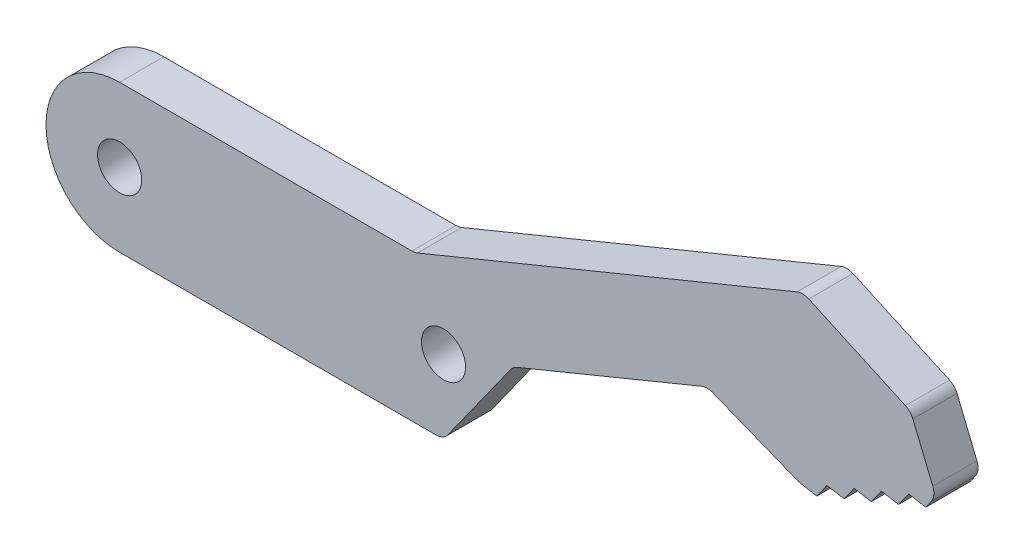
SolidWorks part; units mm, degrees
ref_plane "Front Plane" through (0, 0, 0) normal (0, 0, 1) x (1, 0, 0)
ref_plane "Top Plane" through (0, 0, 0) normal (0, 1, 0) x (1, 0, 0)
ref_plane "Right Plane" through (0, 0, 0) normal (1, 0, 0) x (0, 0, -1)
sketch "Sketch1" plane through (0, 0, 0) normal (0, 0, 1) x (1, 0, 0)
  line L0 (0, 0) -> (22, 0) construction
  line L1 (0, 5) -> (22, 5)
  line L2 (0, -5) -> (22, -5)
  line L3 (20.05, 5) -> (23.9914, -4.5863) construction
  line L4 (20.05, 5) -> (51.4959, 17.929) construction
  line L5 (23.9914, -4.5863) -> (55.4373, 8.3426) construction
  line L6 (51.4959, 17.929) -> (55.4373, 8.3426) construction
  line L7 (20.05, 5) -> (46.409, 15.8375)
  line L8 (46.409, 15.8375) -> (53.7261, 12.5046)
  line L9 (53.7261, 12.5046) -> (55.4373, 8.3426)
  line L10 (55.4373, 8.3426) -> (46.1885, 4.54) construction
  line L11 (46.1885, 4.54) -> (39.9002, 7.0361)
  line L12 (39.9002, 7.0361) -> (26.7299, 1.6211)
  line L13 (46.1885, 4.54) -> (47.3529, 4.3376)
  line L14 (47.3529, 4.3376) -> (48.0382, 5.3005)
  line L15 (47.3529, 4.3376) -> (54.752, 7.3797) construction
  line L16 (48.0382, 5.3005) -> (49.2027, 5.0981)
  line L17 (49.2027, 5.0981) -> (49.888, 6.0611)
  line L18 (49.888, 6.0611) -> (51.0524, 5.8587)
  line L19 (51.0524, 5.8587) -> (51.7378, 6.8216)
  line L20 (51.7378, 6.8216) -> (52.9022, 6.6192)
  line L21 (52.9022, 6.6192) -> (53.5875, 7.5821)
  line L22 (53.5875, 7.5821) -> (54.752, 7.3797)
  line L23 (54.752, 7.3797) -> (55.4373, 8.3426)
  line L24 (26.7299, 1.6211) -> (22, -5)
  arc A0 (0, 5) -> (0, -5) centre (0, 0) ccw
  arc A1 (22, -5) -> (22, 5) centre (22, 0) ccw
  circle A2 centre (0, 0) radius 1.5
  circle A3 centre (22, 0) radius 1.5
  point P3 (11, 0)
  dimension "D11" = 3
  dimension "D1" = 10
  dimension "D2" = 22
  dimension "D3" = 157.65
  dimension "D4" = 1.95
  dimension "D5" = 34
  dimension "D6" = 14.24
  dimension "D7" = 10
  dimension "D8" = 4.5
  dimension "D9" = 5.5
  dimension "D10" = 136
  dimension "D12" = 2
  dimension "D13" = 0.63
  dimension "D14" = 8
extrude "Boss-Extrude1" add sketch "Sketch1" along normal blind 3 contours A1 L1 A0 L2 A3 A2 | A1 L12 L11 L13 L14 L16 L17 L18 L19 L20 L21 L22 L23 L9 L8 L7 L1
fillet "Fillet1" radius 1 8 edges at (46.1885, 4.54, 1.5) (55.4373, 8.3426, 1.5) (53.7261, 12.5046, 1.5) (46.409, 15.8375, 1.5) (20.05, 5, 1.5) (26.7299, 1.6211, 1.5) (39.9002, 7.0361, 1.5) (22, -5, 1.5)
